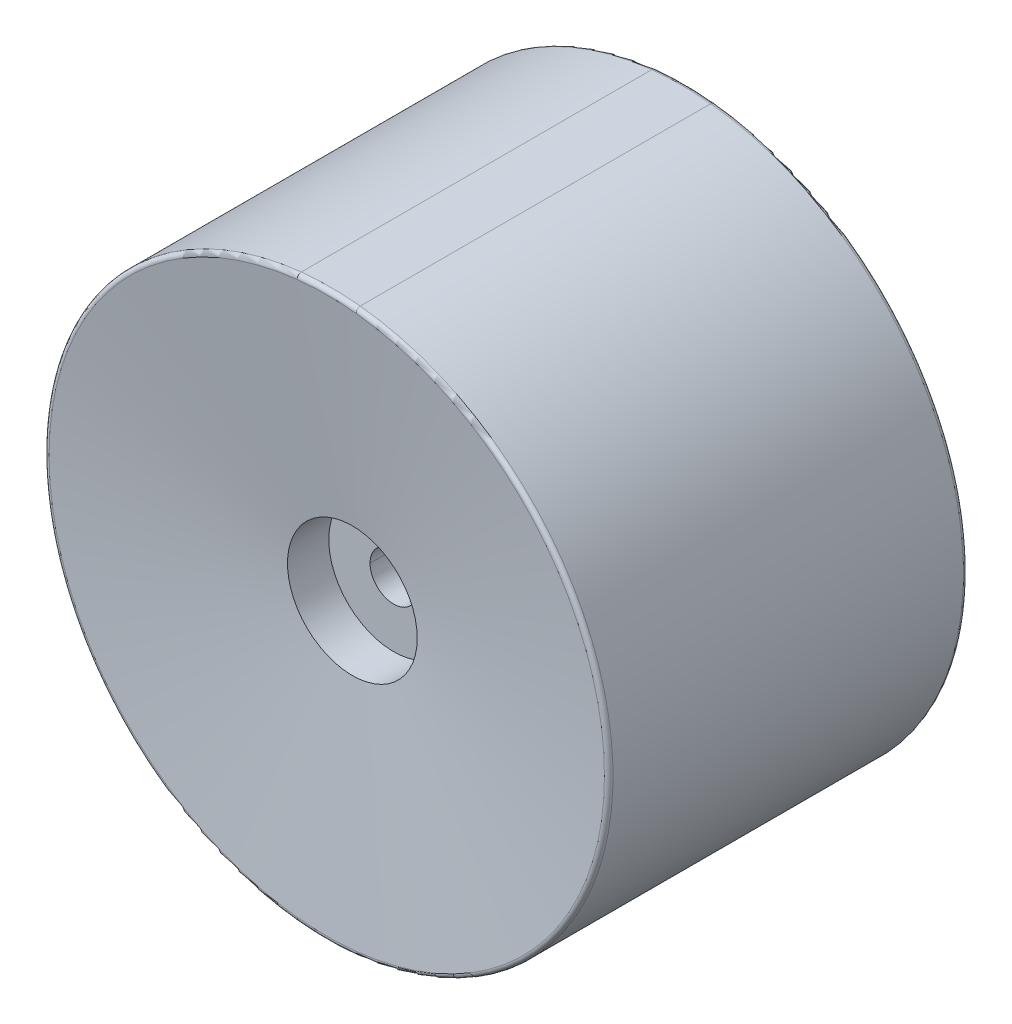
SolidWorks part; units mm, degrees
material "PUR"
ref_plane "Front Plane" through (0, 0, 0) normal (0, 0, 1) x (1, 0, 0)
ref_plane "Top Plane" through (0, 0, 0) normal (0, 1, 0) x (1, 0, 0)
ref_plane "Right Plane" through (0, 0, 0) normal (1, 0, 0) x (0, 0, -1)
sketch "Sketch1" plane through (0, 0, 0) normal (0, 1, 0) x (1, 0, 0)
  line L0 (0, -26.0535) -> (0, 26.0535)
  line L1 (0, 26.0535) -> (11, 26.0535)
  line L3 (0, -26.0535) -> (11, -26.0535)
  line L4 (11, 26.0535) -> (11, -26.0535)
  line L5 (0, 0) -> (11, -26.0535) construction
  line L6 (0, 0) -> (11, 26.0535) construction
  line L7 (0, 0) -> (47.862, 0) construction
  line L8 (47.862, -30.4868) -> (47.862, 30.4869)
  line L9 (11, 26.0535) -> (47.862, 30.4869)
  line L10 (47.862, 30.4869) -> (17.2979, 30.4869) construction
  line L11 (11, -26.0535) -> (47.862, -30.4868)
  line L12 (47.862, -30.4868) -> (-12.6523, -30.4868) construction
  point P0 (0, 0)
  point P9 (0, 0)
  point P12 (47.862, 0)
  point P13 (0, 0)
  dimension "D1" = 11
  dimension "D2" = 47.862
  dimension "D3" = 60.9737
  dimension "D4" = 6.858
revolve "Revolve1" add sketch "Sketch1" angle 360 about L0
sketch "Sketch3" plane through (0, 0, 26.0535) normal (0, 0, 1) x (1, 0, 0)
  circle A0 centre (0, 0) radius 11
extrude "Cut-Extrude1" cut sketch "Sketch3" against normal blind 7
sketch "Sketch4" plane through (0, 0, 19.0535) normal (0, 0, 1) x (1, 0, 0)
  circle A0 centre (0, 0) radius 4
extrude "Cut-Extrude2" cut sketch "Sketch4" against normal through all
sketch "Sketch5" plane through (0, 0, -26.0535) normal (0, 0, -1) x (-1, 0, 0)
  circle A0 centre (0, 0) radius 11
extrude "Cut-Extrude3" cut sketch "Sketch5" against normal blind 7
fillet "Fillet2" radius 0.688 2 edges at (47.862, 0, 30.4868) (47.862, 0, -30.4869)
split line "Split Line1"
sketch "Sketch7" plane through (0, 0, 0) normal (0, 1, 0) x (1, 0, 0)
  line L1 (5, -68.689) -> (-5, -68.689)
  line L2 (5, -68.689) -> (5, 68.689)
  line L3 (5, 68.689) -> (-5, 68.689)
  line L4 (-5, -68.689) -> (-5, 68.689)
  line L5 (5, -68.689) -> (-5, 68.689) construction
  line L6 (5, 68.689) -> (-5, -68.689) construction
  point P0 (0, 0)
  dimension "D1" = 10
split line "Split Line2"
